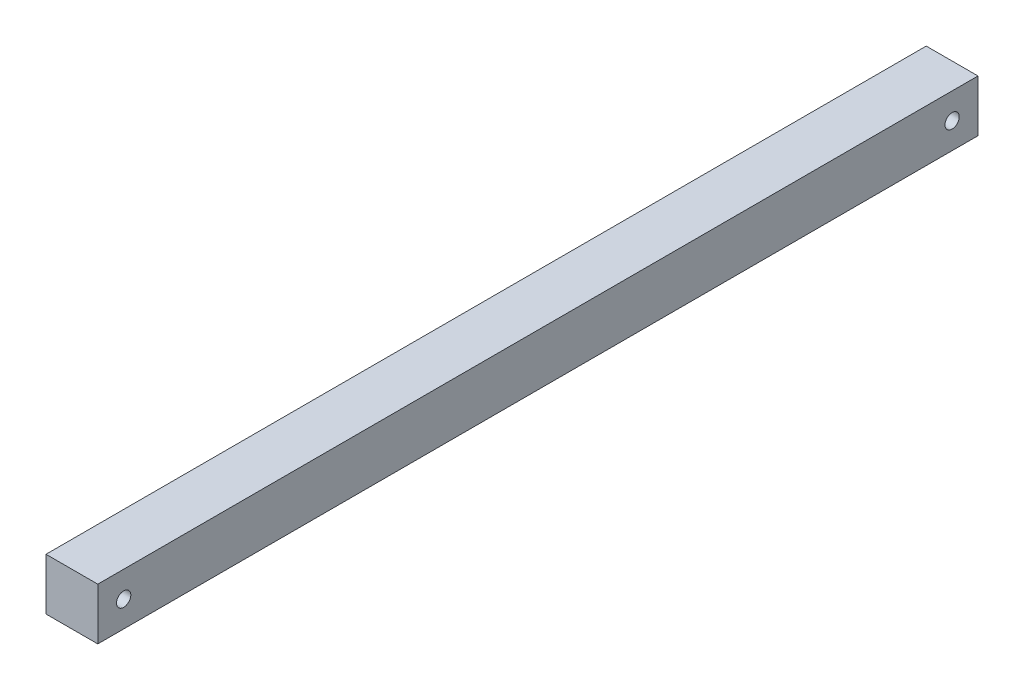
SolidWorks part; units mm, degrees
ref_plane "Front Plane" through (0, 0, 0) normal (0, 0, 1) x (1, 0, 0)
ref_plane "Top Plane" through (0, 0, 0) normal (0, 1, 0) x (1, 0, 0)
ref_plane "Right Plane" through (0, 0, 0) normal (1, 0, 0) x (0, 0, -1)
sketch "Sketch1" plane through (0, 0, 0) normal (0, 0, 1) x (1, 0, 0)
  line L5 (-12.7, -12.7) -> (12.7, -12.7)
  line L6 (-12.7, -12.7) -> (-12.7, 12.7)
  line L7 (-12.7, 12.7) -> (12.7, 12.7)
  line L8 (12.7, -12.7) -> (12.7, 12.7)
  line L9 (-12.7, -12.7) -> (12.7, 12.7) construction
  line L10 (-12.7, 12.7) -> (12.7, -12.7) construction
  point P0 (0, 0)
  dimension "D1" = 25.4
  dimension "D2" = 25.4
extrude "Boss-Extrude1" add sketch "Sketch1" along normal blind 431.8
sketch "Sketch10" plane through (-12.7, 0, 0) normal (-1, 0, 0) x (0, 0, 1)
  line L0 (215.9, 12.7) -> (215.9, 75.2381) construction
  line L1 (431.8, 12.7) -> (0, 12.7) construction
  line L2 (431.8, 12.7) -> (431.8, -12.7) construction
  circle A0 centre (419.1, 0) radius 3.5
  circle A1 centre (12.7, 0) radius 3.5
  dimension "D1" = 7
  dimension "D3" = 12.7
  dimension "D2" = 12.7
extrude "Cut-Extrude6" cut sketch "Sketch10" against normal through all
